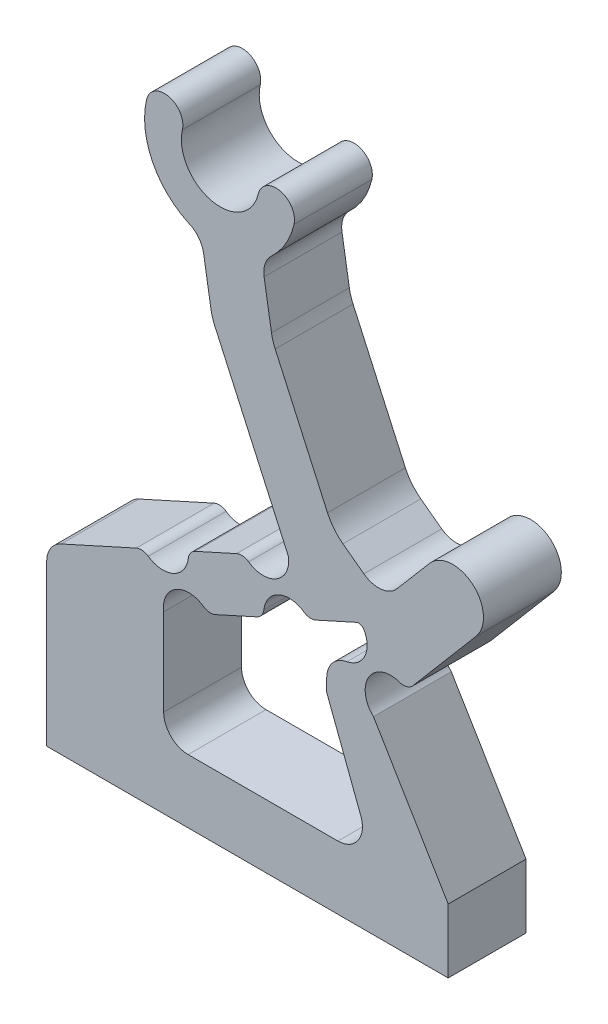
SolidWorks part; units mm, degrees
ref_plane "Front Plane" through (0, 0, 0) normal (0, 0, 1) x (1, 0, 0)
ref_plane "Top Plane" through (0, 0, 0) normal (0, 1, 0) x (1, 0, 0)
ref_plane "Right Plane" through (0, 0, 0) normal (1, 0, 0) x (0, 0, -1)
sketch "Sketch-SkeletonConfigUp" plane through (0, 0, 0) normal (0, 0, 1) x (1, 0, 0)
  line L0 (0, 0) -> (0, -50000) construction
  line L1 (0, 0) -> (5.2694, -4.2823) construction
  line L2 (16.5608, -13.4586) -> (13.0191, -3.4572) construction
  line L3 (13.0191, -3.4572) -> (9.3602, -2.4315) construction
  line L4 (9.3602, -2.4315) -> (5.2694, -4.2823) construction
  line L5 (13.0191, -3.4572) -> (16.5614, 0.711) construction
  line L6 (9.3602, -2.4315) -> (7.0797, 11.4322) construction
  line L7 (5.2694, -4.2823) -> (16.5608, -13.4586) construction
  line L8 (-768.3403, 624.4132) -> (16.5608, -13.4586) construction
  dimension "D2" = 6.79
  dimension "D3" = 14.55
  dimension "D4" = 10.61
  dimension "D5" = 148.6
  dimension "D6" = 3.8
  dimension "D7" = 5.47
  dimension "D8" = 14.05
  dimension "D9" = 4.49
  dimension "D10" = 65.3
  dimension "D11" = 65
  dimension "D12" = 50.9
sketch "Sketch-SkeletonConfigDown" plane through (0, 0, 0) normal (0, 0, 1) x (1, 0, 0)
  line L0 (0, 0) -> (0, -50000) construction
  line L1 (0, 0) -> (5.2694, -4.2823) construction
  line L2 (16.5608, -13.4586) -> (13.0191, -3.4572) construction
  line L3 (13.0191, -3.4572) -> (9.6581, -5.2302) construction
  line L4 (9.6581, -5.2302) -> (5.2694, -4.2823) construction
  line L5 (13.0191, -3.4572) -> (12.7221, 2.0047) construction
  line L6 (9.6581, -5.2302) -> (-1.5351, 3.2618) construction
  line L7 (5.2694, -4.2823) -> (16.5608, -13.4586) construction
  line L8 (-771.7106, 627.1522) -> (16.5608, -13.4586) construction
  dimension "D2" = 6.79
  dimension "D3" = 14.55
  dimension "D4" = 10.61
  dimension "D5" = 148.6
  dimension "D6" = 3.8
  dimension "D7" = 5.47
  dimension "D8" = 14.05
  dimension "D9" = 4.49
  dimension "D10" = 65.3
  dimension "D11" = 65
  dimension "D1" = 50.9
sketch "Sketch-ConfigUp" plane through (0, 0, 0) normal (0, 0, 1) x (1, 0, 0)
  line L1 (8.0369, -1.9326) -> (5.7683, -2.959)
  line L4 (9.3602, -2.4315) -> (5.2694, -4.2823) construction
  line L5 (15.6089, 1.5204) -> (13.6856, -0.7427)
  line L6 (5.2694, -4.2823) -> (16.5608, -13.4586) construction
  line L9 (13.0191, -3.4572) -> (9.3602, -2.4315) construction
  line L11 (6.9026, -2.4458) -> (7.727, -4.268) construction
  line L16 (13.3241, -5.0287) -> (14.6192, -3.5047) construction
  line L17 (17.5139, -0.0985) -> (14.6721, -3.4424)
  line L18 (13.0191, -3.4572) -> (16.5614, 0.711) construction
  line L19 (15.6013, 1.5115) -> (17.5063, -0.1075) construction
  line L20 (6.3045, 8.4436) -> (6.7426, 5.7803)
  line L21 (9.2095, 6.186) -> (8.7714, 8.8493)
  line L22 (9.3602, -2.4315) -> (7.0797, 11.4322) construction
  line L23 (6.0231, 10.1543) -> (8.49, 10.5601) construction
  line L26 (12.3716, -4.2192) -> (9.4385, -7.6705) construction
  line L27 (-155977.6217, 126759.5747) -> (16.5608, -13.4586) construction
  line L30 (10.3474, -5.0569) -> (11.8714, -6.352) construction
  line L38 (5.5133, 11.1745) -> (7.0797, 11.4322) construction
  line L39 (7.0797, 11.4322) -> (10.0861, 10.7293) construction
  line L42 (7.2022, -8.5173) -> (7.2022, -12.9421) construction
  line L43 (12.7142, -1.8857) -> (14.6192, -3.5047) construction
  line L44 (6.1805, -3.8701) -> (4.3583, -4.6945) construction
  line L46 (6.5926, -4.7812) -> (4.7705, -5.6056) construction
  line L47 (11.4191, -3.4097) -> (13.3241, -5.0287) construction
  line L51 (9.2571, -2.2038) -> (9.4632, -2.6593) construction
  line L52 (8.0369, -1.9326) -> (8.8613, -3.7548) construction
  line L53 (9.8591, -1.1082) -> (10.6835, -2.9304) construction
  line L54 (6.1549, -10.1498) -> (6.1549, -12.9421) construction
  line L56 (8.4491, -2.8437) -> (10.2713, -2.0193) construction
  line L59 (9.8591, -1.1082) -> (8.0369, -1.9326) construction
  line L61 (8.8613, -3.7548) -> (6.5926, -4.7812)
  line L62 (5.7683, -2.959) -> (6.5926, -4.7812) construction
  line L67 (7.0797, 11.4322) -> (4.0733, 12.135) construction
  line L69 (13.2096, -3.6191) -> (12.8286, -3.2953) construction
  line L71 (14.6192, -3.5047) -> (15.6685, -2.2699) construction
  line L73 (5.7683, -2.959) -> (3.9461, -3.7834) construction
  line L77 (9.4385, -7.6705) -> (16.5608, -13.4586) construction
  line L81 (12.3716, -4.2192) -> (13.6667, -2.6952) construction
  line L82 (15.6013, 1.5115) -> (13.6856, -0.7427) construction
  line L93 (5.1663, -4.0545) -> (5.3724, -4.5101) construction
  line L108 (0, -5.5687) -> (0, -12.7382)
  line L115 (3.9461, -3.7834) -> (0, -5.5687)
  line L117 (11.4191, -3.4097) -> (12.7142, -1.8857) construction
  line L121 (10.6835, -2.9304) -> (8.8613, -3.7548) construction
  line L125 (4.7705, -5.6056) -> (4.7705, -10.1498)
  line L128 (0, -12.7382) -> (16.3721, -12.7382)
  line L129 (3.9461, -3.7834) -> (4.7705, -5.6056) construction
  line L131 (0, -10.1498) -> (16.3859, -10.1498) construction
  line L132 (0, 200000) -> (0, -250000) construction
  line L133 (13.3241, -5.0287) -> (13.3241, -10.1498) construction
  line L134 (11.4191, -3.4097) -> (11.4191, -5.1284)
  line L135 (11.4191, -10.1498) -> (6.1549, -10.1498)
  line L136 (13.3241, -10.1498) -> (13.3241, -12.9421) construction
  line L137 (4.7705, -10.1498) -> (6.1549, -10.1498)
  line L138 (13.6856, -0.7427) -> (12.7142, -1.8857) construction
  line L140 (13.3241, -5.0287) -> (16.3721, -10.1267)
  line L141 (16.3721, -10.1267) -> (16.3721, -12.7382)
  line L143 (11.4191, -5.1284) -> (13.3241, -10.1498)
  line L144 (13.3241, -10.1498) -> (11.4191, -10.1498)
  line L145 (11.4191, -5.1284) -> (11.4191, -10.1498) construction
  line L146 (9.8591, -1.1082) -> (12.7142, -1.8857) construction
  line L149 (11.6652, 0.7579) -> (13.6856, -0.7427)
  line L152 (10.6835, -2.9304) -> (12.8032, -1.9714)
  line L154 (9.8591, -1.1082) -> (6.7426, 5.7803)
  line L156 (6.7426, 5.7803) -> (9.2095, 6.186) construction
  line L157 (9.2095, 6.186) -> (11.6652, 0.7579)
  arc A0 (15.6089, 1.5204) -> (17.5139, -0.0985) centre (16.5614, 0.711) cw
  arc A2 (5.5339, 11.7936) -> (8.6255, 11.0708) centre (7.0797, 11.4322) ccw
  arc A3 (8.7714, 8.8493) -> (10.0861, 10.7293) centre (7.0797, 11.4322) ccw
  arc A4 (4.0733, 12.135) -> (5.5339, 11.7936) centre (4.8036, 11.9643) cw
  arc A5 (10.0861, 10.7293) -> (8.6255, 11.0708) centre (9.3558, 10.9) ccw
  arc A6 (4.0733, 12.135) -> (6.3045, 8.4436) centre (7.0797, 11.4322) ccw
  arc A7 (8.8613, -3.7548) -> (10.6835, -2.9304) centre (9.8926, -3.6084) cw
  arc A15 (6.5926, -4.7812) -> (4.7705, -5.6056) centre (5.8018, -5.4591) ccw
  arc A21 (8.0369, -1.9326) -> (9.8591, -1.1082) centre (8.8278, -1.2547) ccw
  arc A42 (5.7683, -2.959) -> (3.9461, -3.7834) centre (4.7369, -3.1055) cw
  arc A43 (13.3241, -5.0287) -> (14.6721, -3.4424) centre (14.0292, -4.262) cw
  arc A44 (11.4191, -3.4097) -> (12.8032, -1.9714) centre (12.0666, -2.6477) ccw
  point P27 (7.3148, -3.3569)
  point P38 (16.5538, 0.702)
  point P51 (7.2565, 10.3572)
  point P61 (11.1094, -5.7044)
  point P125 (5.3724, -4.5101)
  point P130 (5.1663, -4.0545)
  dimension "D3" = 3.175
  dimension "D4" = 6.175
  dimension "D14" = 22.5
  dimension "D21" = 22.5
  dimension "D22" = 2
  dimension "D24" = 0.5
  dimension "D9" = 2
  dimension "D10" = 2
  dimension "D11" = 0.5
  dimension "D6" = 2
  dimension "D7" = 0.5
  dimension "D16" = 2.5
  dimension "D5" = 1.5
  dimension "D8" = 16
extrude "Boss-ConfigUp" add sketch "Sketch-ConfigUp" along normal mid plane 3.175
fillet "Fillet1" radius 1 4 edges at (8.7714, 8.8493, 0) (6.3045, 8.4436, 0) (0, -5.5687, 0) (13.6856, -0.7427, 0)
fillet "Fillet2" radius 1 1 edges at (11.4191, -3.4097, 0)
fillet "Fillet3" radius 0.5 7 edges at (14.6721, -3.4424, 0) (3.9461, -3.7834, 0) (6.5926, -4.7812, 0) (8.8613, -3.7548, 0) (8.0369, -1.9326, 0) (5.7683, -2.959, 0) (10.6835, -2.9304, 0)
fillet "Fillet4" radius 0.25 2 edges at (9.8591, -1.1082, 0) (12.8032, -1.9714, 0)
fillet "Fillet5" radius 2 3 edges at (11.6652, 0.7579, 0) (9.2095, 6.186, 0) (6.7426, 5.7803, 0)
fillet "Fillet7" radius 1 2 edges at (13.3241, -10.1498, 0) (4.7705, -10.1498, 0)
equation "\"axle-diameter\"=2"
equation "\"switch-thickness\"=12"
equation "\"base-width\"=4.0"
equation "\"axle-bushing-radius\"=3"
equation "\"clearance\"= 0.25"
equation "\"arm-width\"=1.5"
equation "\"min-diameter\"=70"
equation "\"alpha\"=50.9"
equation "\"beta\"=26.83"
equation "\"gamma\"=148.6"
equation "\"delta\"=65.0"
equation "\"epsilon\"=65.3"
equation "\"eta\"=-261.68"
equation "\"l_AB\"=14.55"
equation "\"l_AC\"=4.49"
equation "\"l_BD\"=10.61"
equation "\"l_CD\"=3.80"
equation "\"l_CE\"=14.05"
equation "\"l_DF\"=5.47"
equation "\"l_OA\"=6.79"
equation "\"D2@Sketch-SkeletonConfigUp\" = \"l_OA\""
equation "\"D3@Sketch-SkeletonConfigUp\" = \"l_AB\""
equation "\"D4@Sketch-SkeletonConfigUp\" = \"l_BD\""
equation "\"D5@Sketch-SkeletonConfigUp\" = \"gamma\""
equation "\"D6@Sketch-SkeletonConfigUp\" = \"l_CD\""
equation "\"D7@Sketch-SkeletonConfigUp\" = \"l_DF\""
equation "\"D8@Sketch-SkeletonConfigUp\" = \"l_CE\""
equation "\"D9@Sketch-SkeletonConfigUp\" = \"l_AC\""
equation "\"D_groove\"=3.175"
equation "\"D7@Sketch-SkeletonConfigDown\" = \"l_DF\""
equation "\"D6@Sketch-SkeletonConfigDown\" = \"l_CD\""
equation "\"D2@Sketch-SkeletonConfigDown\" = \"l_OA\""
equation "\"D3@Sketch-SkeletonConfigDown\" = \"l_AB\""
equation "\"D9@Sketch-SkeletonConfigDown\" = \"l_AC\""
equation "\"D8@Sketch-SkeletonConfigDown\" = \"l_CE\""
equation "\"D5@Sketch-SkeletonConfigDown\" = \"gamma\""
equation "\"D4@Sketch-SkeletonConfigDown\" = \"l_BD\""
equation "\"D1@Sketch-SkeletonConfigDown\" = \"alpha\""
equation "\"hinge_length\"=1.5"
equation "\"hinge_depth\"=0.25"
equation "\"D10@Sketch-SkeletonConfigUp\"=\"epsilon\""
equation "\"D11@Sketch-SkeletonConfigUp\"=\"delta\""
equation "\"D12@Sketch-SkeletonConfigUp\"=\"alpha\""
equation "\"D11@Sketch-SkeletonConfigDown\"=\"delta\""
equation "\"D10@Sketch-SkeletonConfigDown\"=\"epsilon\""
equation "\"EE_dx\"=8.64"
equation "\"EE_dy\"=8.19"
equation "\"r_groove\"=\"D_groove\"/2"
equation "\"t_wall\"=25.4/16"
equation "\"width_lower\"=\"D_groove\"+\"t_wall\""
equation "\"cable_to_bottom\"=30.6257"
equation "\"switch_EE-up_base_dy\"=24"
equation "\"switch_EE-down_base_dy\"=16"
equation "\"D8@Sketch-ConfigUp\"=\"switch_EE-down_base_dy\""
